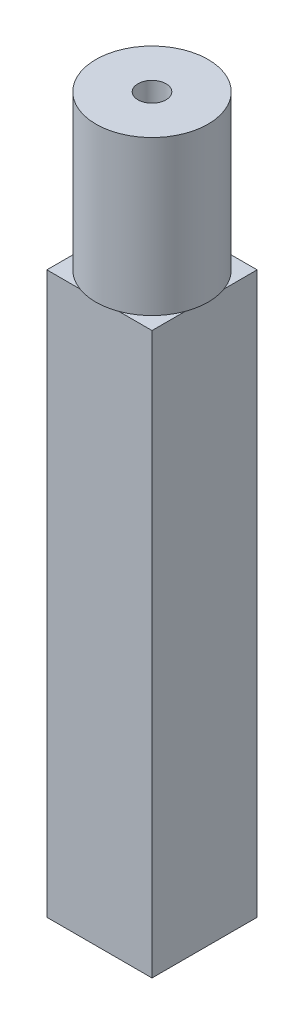
SolidWorks part; units mm, degrees
ref_plane "前视基准面" through (0, 0, 0) normal (0, 0, 1) x (1, 0, 0)
ref_plane "上视基准面" through (0, 0, 0) normal (0, 1, 0) x (1, 0, 0)
ref_plane "右视基准面" through (0, 0, 0) normal (1, 0, 0) x (0, 0, -1)
sketch "草图1" plane through (0, 0, 0) normal (0, 1, 0) x (1, 0, 0)
  circle A0 centre (0, 0) radius 8
extrude "凸台-拉伸1" add sketch "草图1" along normal blind 22
sketch "草图2" plane through (0, 0, 0) normal (0, -1, 0) x (1, 0, 0)
  line L0 (-7.5, 7.5) -> (7.5, 7.5)
  line L1 (-7.5, 7.5) -> (-7.5, -7.5)
  line L2 (7.5, 7.5) -> (7.5, -7.5)
  line L3 (-7.5, -7.5) -> (7.5, -7.5)
  point P1 (0, 0)
extrude "凸台-拉伸2" add sketch "草图2" along normal blind 80
sketch "草图3" plane through (0, 22, 0) normal (0, 1, 0) x (1, 0, 0)
  circle A0 centre (0, 0) radius 2
extrude "切除-拉伸1" cut sketch "草图3" against normal blind 11
